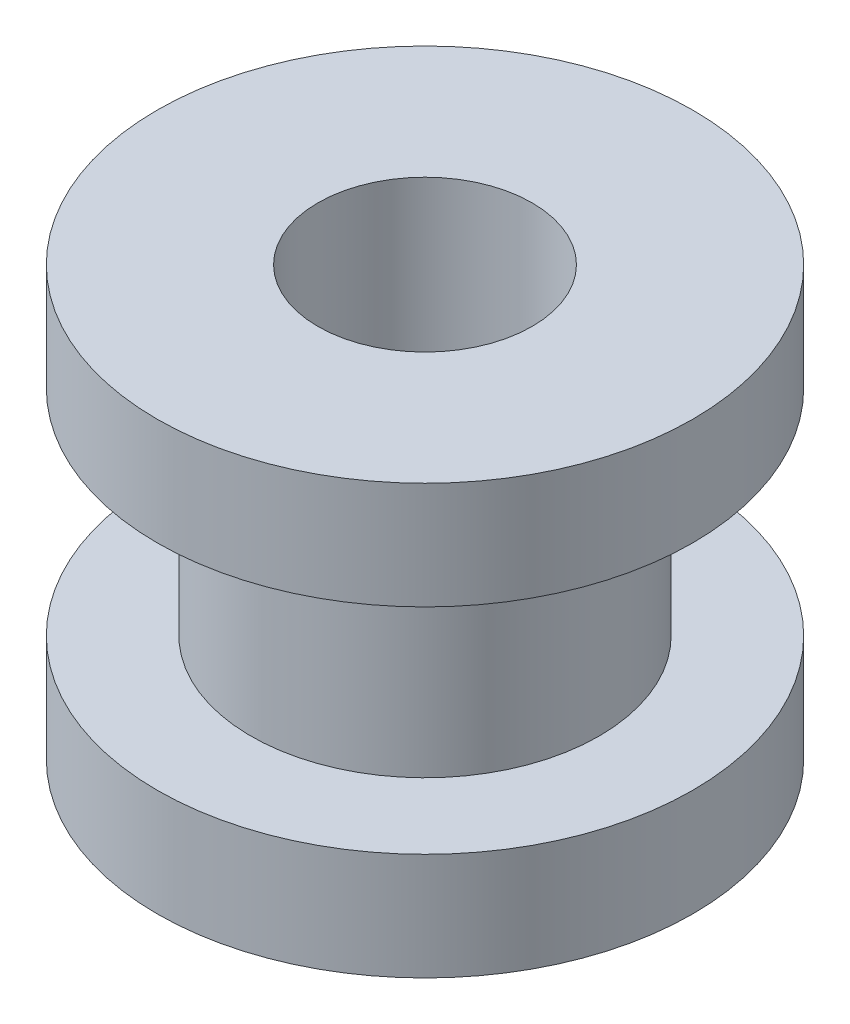
SolidWorks part; units mm, degrees
ref_plane "Front Plane" through (0, 0, 0) normal (0, 0, 1) x (1, 0, 0)
ref_plane "Top Plane" through (0, 0, 0) normal (0, 1, 0) x (1, 0, 0)
ref_plane "Right Plane" through (0, 0, 0) normal (1, 0, 0) x (0, 0, -1)
sketch "Sketch2" plane through (0, 0, 0) normal (0, 0, 1) x (1, 0, 0)
  line L0 (2, 4) -> (2, -4)
  line L1 (2, -4) -> (5, -4)
  line L2 (5, -4) -> (5, -2)
  line L3 (5, -2) -> (3.25, -2)
  line L4 (3.25, -2) -> (3.25, 2)
  line L5 (3.25, 2) -> (5, 2)
  line L6 (5, 2) -> (5, 4)
  line L7 (5, 4) -> (2, 4)
  line L8 (0, -211.4764) -> (0, 10362.3416) construction
  point P9 (2, 0)
  dimension "D1" = 4
  dimension "D2" = 10
  dimension "D3" = 1.75
  dimension "D4" = 2
  dimension "D5" = 4
  dimension "D6" = 2
revolve "Revolve1" add sketch "Sketch2" angle 360 about L8
